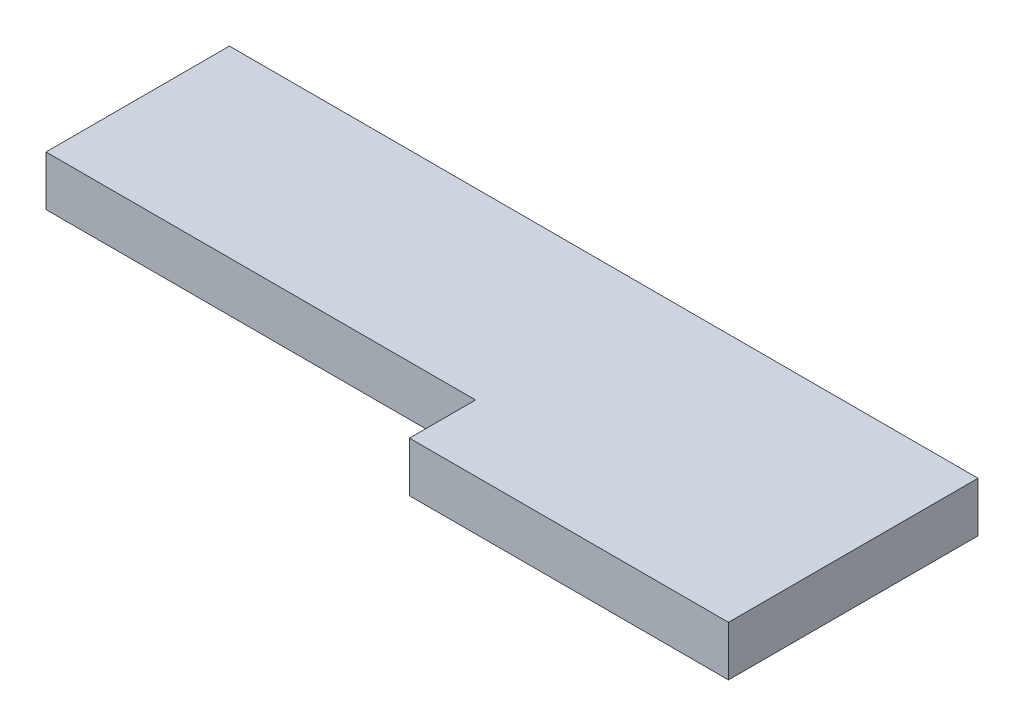
SolidWorks part; units mm, degrees
ref_plane "Front Plane" through (0, 0, 0) normal (0, 0, 1) x (1, 0, 0)
ref_plane "Top Plane" through (0, 0, 0) normal (0, 1, 0) x (1, 0, 0)
ref_plane "Right Plane" through (0, 0, 0) normal (1, 0, 0) x (0, 0, -1)
sketch "Sketch1" plane through (0, 0, 0) normal (0, 1, 0) x (1, 0, 0)
  line L0 (-123.913, -0.9511) -> (-123.913, -37.7073)
  line L2 (26.087, -50.9511) -> (26.087, -0.9511)
  line L3 (26.087, -0.9511) -> (-123.913, -0.9511)
  line L6 (-37.8369, -37.7073) -> (-37.8369, -50.9511)
  line L7 (-37.8369, -50.9511) -> (26.087, -50.9511)
  line L8 (-123.913, -37.7073) -> (-37.8369, -37.7073)
extrude "Boss-Extrude1" add sketch "Sketch1" along normal blind 10
